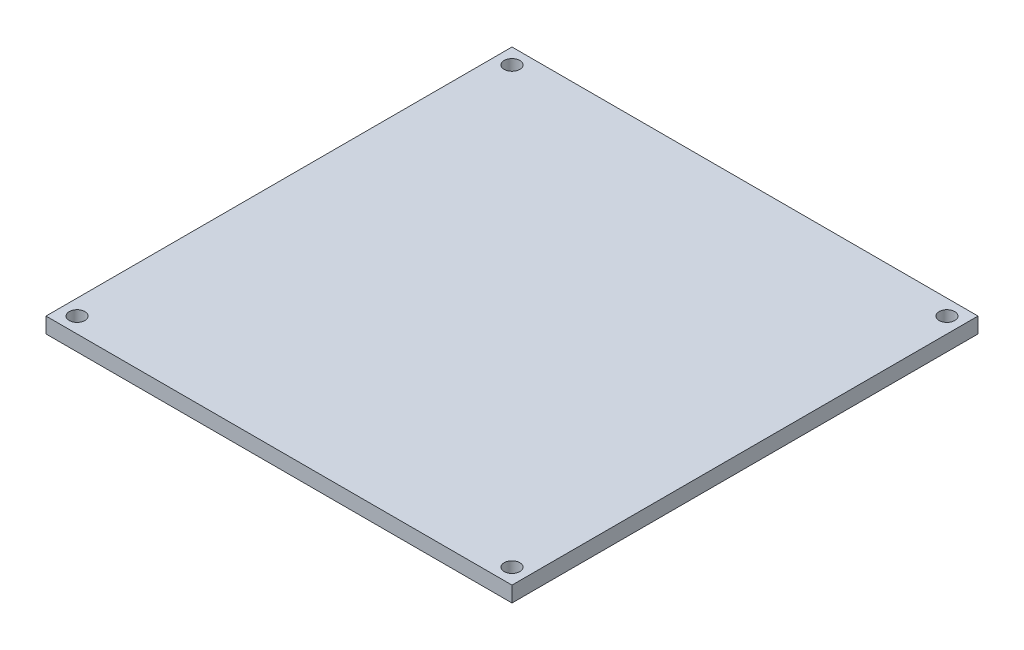
SolidWorks part; units mm, degrees
ref_plane "Front Plane" through (0, 0, 0) normal (0, 0, 1) x (1, 0, 0)
ref_plane "Top Plane" through (0, 0, 0) normal (0, 1, 0) x (1, 0, 0)
ref_plane "Right Plane" through (0, 0, 0) normal (1, 0, 0) x (0, 0, -1)
sketch "Sketch1" plane through (0, 0, 0) normal (0, 1, 0) x (1, 0, 0)
  line L0 (1.5, 1.5) -> (1.5, 43.5) construction
  line L1 (0, 0) -> (45, 0)
  line L2 (0, 0) -> (0, 45)
  line L3 (0, 45) -> (45, 45)
  line L4 (45, 0) -> (45, 45)
  line L5 (1.5, 43.5) -> (43.5, 43.5) construction
  line L6 (43.5, 43.5) -> (43.5, 1.5) construction
  line L7 (1.5, 1.5) -> (43.5, 1.5) construction
  line L8 (0, 22.5) -> (45, 22.5) construction
  circle A0 centre (1.5, 1.5) radius 0.7541
  circle A1 centre (1.5, 43.5) radius 0.7541
  circle A2 centre (43.5, 43.5) radius 0.7541
  circle A3 centre (43.5, 1.5) radius 0.7541
  dimension "D1" = 42
  dimension "D2" = 42
  dimension "D5" = 1.5
  dimension "D3" = 1.5
  dimension "D4" = 45
  dimension "D6" = 45
extrude "Boss-Extrude1" add sketch "Sketch1" along normal blind 1.5
